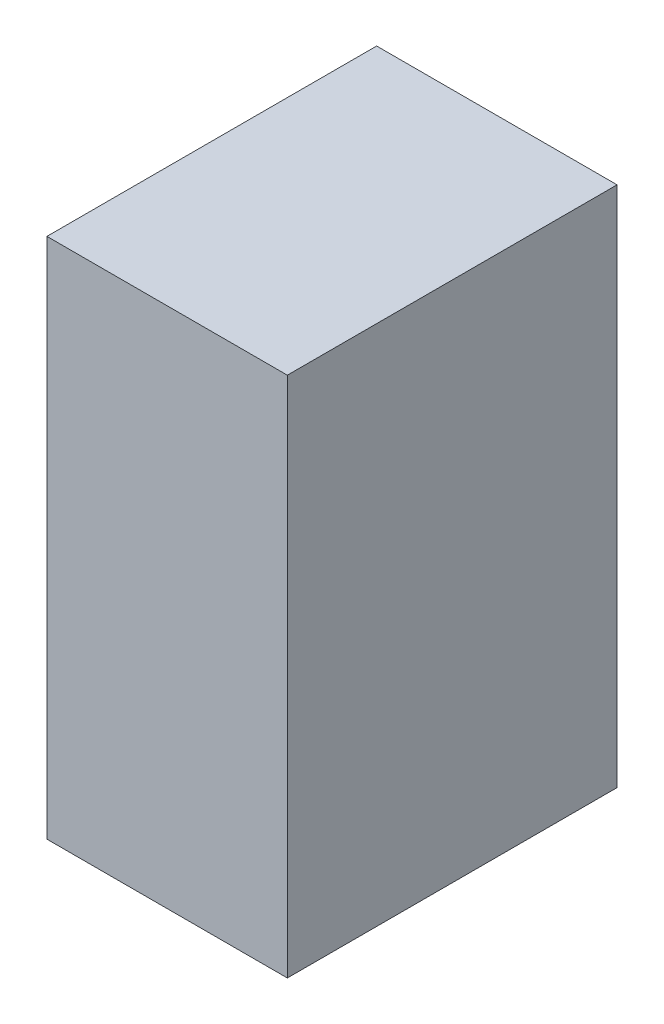
SolidWorks part; units mm, degrees
ref_plane "Alzado" through (0, 0, 0) normal (0, 0, 1) x (1, 0, 0)
ref_plane "Planta" through (0, 0, 0) normal (0, 1, 0) x (1, 0, 0)
ref_plane "Vista lateral" through (0, 0, 0) normal (1, 0, 0) x (0, 0, -1)
sketch "Croquis1" plane through (0, 0, 0) normal (0, 1, 0) x (1, 0, 0)
  line L1 (-17.5, -24) -> (17.5, -24)
  line L2 (-17.5, -24) -> (-17.5, 24)
  line L3 (-17.5, 24) -> (17.5, 24)
  line L4 (17.5, -24) -> (17.5, 24)
  line L5 (-17.5, -24) -> (17.5, 24) construction
  line L6 (-17.5, 24) -> (17.5, -24) construction
  point P0 (0, 0)
  dimension "D1" = 35
  dimension "D2" = 48
extrude "Saliente-Extruir1" add sketch "Croquis1" along normal blind 76
